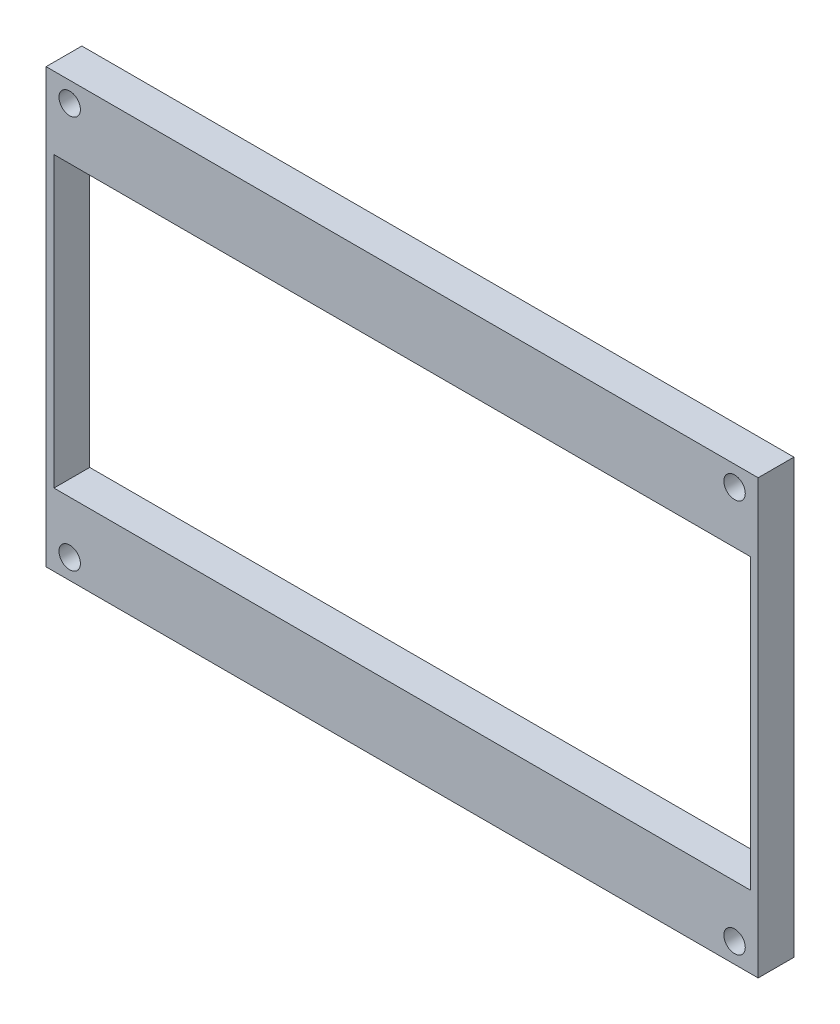
SolidWorks part; units mm, degrees
ref_plane "Plano frontal" through (0, 0, 0) normal (0, 0, 1) x (1, 0, 0)
ref_plane "Plano superior" through (0, 0, 0) normal (0, 1, 0) x (1, 0, 0)
ref_plane "Plano direito" through (0, 0, 0) normal (1, 0, 0) x (0, 0, -1)
sketch "Esboço1" plane through (0, 0, 0) normal (0, 0, 1) x (1, 0, 0)
  line L17 (-26.8, -5.8) -> (72.8, -5.8)
  line L18 (72.8, -5.8) -> (72.8, 54.8)
  line L19 (-26.8, 54.8) -> (-26.8, -5.8)
  line L20 (72.8, 54.8) -> (-26.8, 54.8)
  line L26 (-25.7, 4.3) -> (71.7, 4.3)
  line L27 (-25.7, 44.7) -> (-25.7, 4.3)
  line L28 (71.7, 44.7) -> (-25.7, 44.7)
  line L29 (71.7, 4.3) -> (71.7, 44.7)
  circle A8 centre (-23.5, -3) radius 1.5
  circle A9 centre (69.5, -3) radius 1.5
  circle A10 centre (69.5, 52) radius 1.5
  circle A11 centre (-23.5, 52) radius 1.5
extrude "Ressalto-extrusão1" add sketch "Esboço1" along normal blind 5
